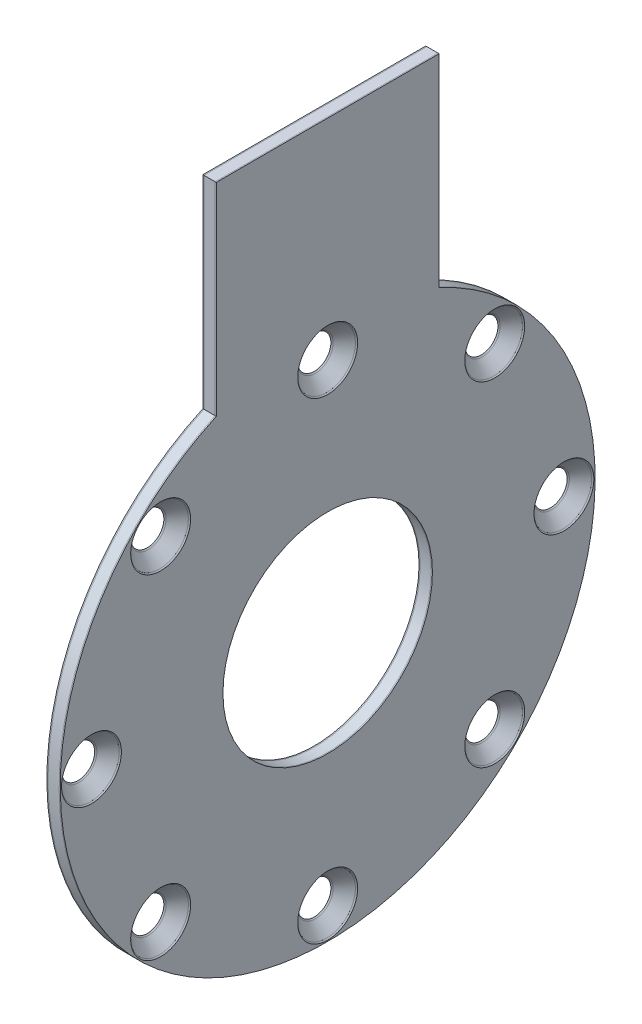
SolidWorks part; units mm, degrees
ref_plane "Front Plane" through (0, 0, 0) normal (0, 0, 1) x (1, 0, 0)
ref_plane "Top Plane" through (0, 0, 0) normal (0, 1, 0) x (1, 0, 0)
ref_plane "Right Plane" through (0, 0, 0) normal (1, 0, 0) x (0, 0, -1)
sketch "Sketch1" plane through (0, 0, 0) normal (1, 0, 0) x (0, 0, -1)
  line L0 (-25, 100) -> (25, 100)
  line L1 (-25, 100) -> (-25, 54.5436)
  line L2 (25, 100) -> (25, 54.5436)
  circle A0 centre (0, 0) radius 60
  circle A1 centre (0, 0) radius 23.5
  point P7 (0, 100)
  dimension "D1" = 120
  dimension "D2" = 47
  dimension "D3" = 40
  dimension "D4" = 50
extrude "Boss-Extrude1" add sketch "Sketch1" along normal blind 0.25 contours A0 L2 L0 L1 | A0 A1
sketch "Sketch4" plane through (0, 0, 0) normal (-1, 0, 0) x (0, 0, 1)
  line L3 (25, 54.5436) -> (25, 100)
  line L4 (25, 100) -> (-25, 100)
  line L5 (-25, 100) -> (-25, 54.5436)
  line L6 (25, 54.5436) -> (25, 100)
  line L7 (25, 100) -> (-25, 100)
  line L8 (-25, 100) -> (-25, 54.5436)
  circle A0 centre (0, 0) radius 23.5 construction
  arc A1 (-25, 54.5436) -> (25, 54.5436) centre (0, 0) ccw
  arc A2 (-25, 54.5436) -> (25, 54.5436) centre (0, 0) ccw
  circle A3 centre (0, 0) radius 23.5
  dimension "D1" = 0
extrude "Boss-Extrude4" add sketch "Sketch4" along normal blind 2.5 separate body
sketch "Sketch5" plane through (-2.5, 0, 0) normal (-1, 0, 0) x (0, 0, 1)
  line L3 (25, 54.5436) -> (25, 100)
  line L4 (25, 100) -> (-25, 100)
  line L5 (-25, 100) -> (-25, 54.5436)
  line L6 (25, 54.5436) -> (25, 100)
  line L7 (25, 100) -> (-25, 100)
  line L8 (-25, 100) -> (-25, 54.5436)
  circle A0 centre (0, 0) radius 23.5 construction
  arc A1 (-25, 54.5436) -> (25, 54.5436) centre (0, 0) ccw
  arc A2 (-25, 54.5436) -> (25, 54.5436) centre (0, 0) ccw
  circle A3 centre (0, 0) radius 23.5
  dimension "D1" = 0
extrude "Boss-Extrude5" add sketch "Sketch5" along normal blind 0.25 separate body contours A2 L6 L7 L8
sketch "Sketch9" plane through (0.25, 0, 0) normal (1, 0, 0) x (0, 0, -1)
  circle A0 centre (0, 0) radius 53
  point P3 (53, 0)
  point P6 (37.4767, -37.4767)
  point P7 (0, -53)
  point P8 (-37.4767, -37.4767)
  point P9 (-53, 0)
  point P10 (-37.4767, 37.4767)
  point P11 (0, 53)
  point P12 (37.4767, 37.4767)
  dimension "D1" = 106
  dimension "D2" = 8
hole_wizard "CSK for M6 Hex Socket Countersunk Cap Screw2" positions "Sketch9" profile "Sketch10" countersink size "M6" standard "ISO" end condition through all
sketch "Sketch10" plane through (0.25, 37.4767, -37.4767) normal (0, 1, 0) x (0, 0, -1)
  line L0 (0, 0) -> (0, 3)
  line L1 (0, 3) -> (3.3, 3)
  line L2 (3.3, 3) -> (3.3, 3.42)
  line L3 (3.3, 3.42) -> (6.72, 0)
  line L5 (6.72, 0) -> (0, 0)
  line L6 (-3.3, 3.42) -> (-6.72, 0) construction
  line L11 (0, -6.35) -> (0, 107.95) construction
  dimension "Thru Hole Dia." = 6.6
  dimension "Thru Hole Depth" = 3
  dimension "Near C'Sink Dia." = 13.44
  dimension "Near C'Sink Angle" = 90
